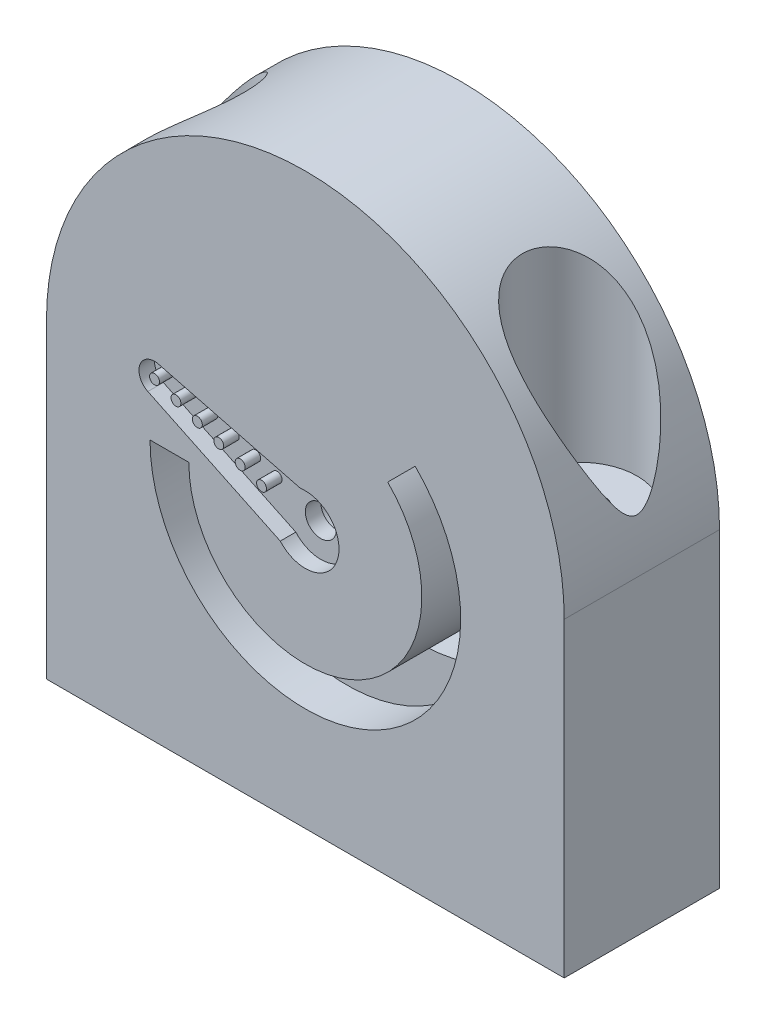
SolidWorks part; units mm, degrees
material "ABS"
ref_plane "Ön Düzlem" through (0, 0, 0) normal (0, 0, 1) x (1, 0, 0)
ref_plane "Üst Düzlem" through (0, 0, 0) normal (0, 1, 0) x (1, 0, 0)
ref_plane "Sağ Düzlem" through (0, 0, 0) normal (1, 0, 0) x (0, 0, -1)
sketch "Sketch1" plane through (0, 0, 0) normal (0, 0, 1) x (1, 0, 0)
  line L0 (-25, 0) -> (-25, -30)
  line L1 (-25, -30) -> (25, -30)
  line L2 (25, -30) -> (25, 0)
  arc A0 (25, 0) -> (-25, 0) centre (0, 0) ccw
  dimension "D1" = 30
  dimension "D3" = 25
  dimension "D2" = 50
extrude "Boss-Extrude1" add sketch "Sketch1" along normal blind 15 contours A0 L0 L1 L2
sketch "Sketch2" plane through (0, 0, 15) normal (0, 0, 1) x (1, 0, 0)
  line L0 (0, 0) -> (0, -5)
  line L1 (-15, -5) -> (-11.25, -5)
  line L2 (7.955, 2.955) -> (10.6066, 5.6066)
  arc A0 (-11.25, -5) -> (7.955, 2.955) centre (0, -5) ccw
  arc A1 (-15, -5) -> (10.6066, 5.6066) centre (0, -5) ccw
extrude "Cut-Extrude1" cut sketch "Sketch2" against normal up to next contours A0 L2 A1 L1
sketch "Sketch3" plane through (0, 0, 15) normal (0, 0, 1) x (1, 0, 0)
  line L0 (0, -5) -> (-21.0777, -5) construction
  line L1 (0, -5) -> (-21.7833, 2.9285) construction
  line L2 (-14.191, 1.7539) -> (-0.462, -1.783)
  line L3 (-15.2123, -1.052) -> (-2.4218, -7.1674)
  arc A1 (-2.4218, -7.1674) -> (-0.462, -1.783) centre (0, -5) ccw
  arc A4 (-14.191, 1.7539) -> (-15.2123, -1.052) centre (-14.5652, 0.3013) ccw
  dimension "D1" = 20
  dimension "D2" = 15.5
  dimension "D3" = 3
  dimension "D5" = 6.5
extrude "Cut-Extrude2" cut sketch "Sketch3" against normal blind 1.5 contours L3 A1 L2 A4
sketch "Sketch4" plane through (0, 0, 13.5) normal (0, 0, 1) x (1, 0, 0)
  circle A0 centre (0, -5) radius 1.5
  dimension "D1" = 3
extrude "Cut-Extrude3" cut sketch "Sketch4" against normal up to next
sketch "Sketch5" plane through (0, 0, 0) normal (0, 0, -1) x (-1, 0, 0)
  circle A0 centre (0, -5) radius 2.5
  dimension "D1" = 5
extrude "Cut-Extrude4" cut sketch "Sketch5" against normal offset from surface (12 mm away) 1.5 up to face at (1.5, -5, 13.5)
sketch "Sketch6" plane through (0, 0, 13.5) normal (0, 0, 1) x (1, 0, 0)
  line L0 (-14.5652, 0.3013) -> (-4.2286, -3.4609) construction
  circle A0 centre (-14.5652, 0.3013) radius 0.48
  circle A1 centre (-12.4979, -0.4511) radius 0.48
  circle A2 centre (-10.4306, -1.2036) radius 0.48
  circle A3 centre (-8.3633, -1.956) radius 0.48
  circle A4 centre (-6.2959, -2.7085) radius 0.48
  circle A5 centre (-4.2286, -3.4609) radius 0.48
  dimension "D1" = 6
  dimension "D2" = 0.96
  dimension "D3" = 11
extrude "Boss-Extrude2" add sketch "Sketch6" along normal blind 1.5
sketch "Sketch7" plane through (0, -30, 0) normal (0, -1, 0) x (1, 0, 0)
  line L2 (0, 0) -> (0, 18.5313) construction
  circle A0 centre (-19, 7.5) radius 2.25
  circle A1 centre (19, 7.5) radius 2.25
  dimension "D2" = 4.5
extrude "Cut-Extrude5" cut sketch "Sketch7" against normal up to next
ref_plane "Plane1" through (0, 23.4671, 0) normal (0, 1, 0) x (1, 0, 0)
sketch "Sketch8" plane through (0, 23.4671, 0) normal (0, 1, 0) x (1, 0, 0)
  line L0 (0, 0) -> (0, -22.7462) construction
  circle A0 centre (-19, -7.5) radius 5.54
  circle A1 centre (19, -7.5) radius 5.54
  dimension "D1" = 11.08
extrude "Cut-Extrude6" cut sketch "Sketch8" against normal blind 21
sketch "Sketch9" plane through (0, -30, 0) normal (0, -1, 0) x (1, 0, 0)
  line L0 (0, 0) -> (0, 15) construction
  line L1 (-25, 15) -> (25, 15) construction
  line L3 (-12, 11) -> (12, 11)
  line L4 (-12, 11) -> (-12, 4)
  line L5 (-12, 4) -> (12, 4)
  line L6 (12, 11) -> (12, 4)
  line L7 (-12, 11) -> (12, 4) construction
  line L8 (-12, 4) -> (12, 11) construction
  point P6 (0, 7.5)
  dimension "D1" = 7
  dimension "D2" = 24
extrude "Cut-Extrude7" cut sketch "Sketch9" against normal up to next
